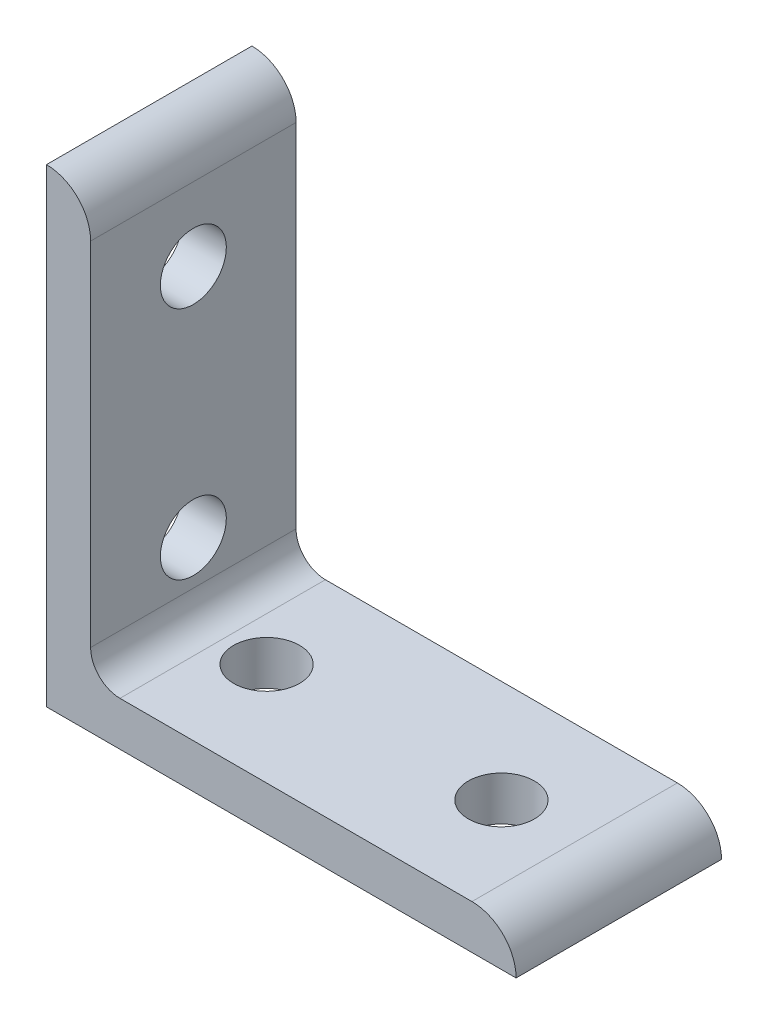
SolidWorks part; units mm, degrees
ref_plane "Front Plane" through (0, 0, 0) normal (0, 0, 1) x (1, 0, 0)
ref_plane "Top Plane" through (0, 0, 0) normal (0, 1, 0) x (1, 0, 0)
ref_plane "Right Plane" through (0, 0, 0) normal (1, 0, 0) x (0, 0, -1)
sketch "Sketch1" plane through (0, 0, 0) normal (0, 0, 1) x (1, 0, 0)
  line L0 (0, 0) -> (0, 50.8)
  line L1 (4.7752, 46.0248) -> (4.7752, 50.8) construction
  line L2 (4.7752, 46.0248) -> (4.7752, 7.9502)
  line L3 (7.9502, 4.7752) -> (46.0248, 4.7752)
  line L4 (4.7752, 50.8) -> (0, 50.8) construction
  line L5 (50.8, 0) -> (0, 0)
  line L6 (46.0248, 4.7752) -> (50.8, 4.7752) construction
  line L7 (50.8, 4.7752) -> (50.8, 0) construction
  arc A0 (4.7752, 46.0248) -> (0, 50.8) centre (0, 46.0248) ccw
  arc A1 (50.8, 0) -> (46.0248, 4.7752) centre (46.0248, 0) ccw
  arc A2 (4.7752, 7.9502) -> (7.9502, 4.7752) centre (7.9502, 7.9502) ccw
  point P10 (4.7752, 48.4124)
  dimension "E" = 3.175
  dimension "D" = 4.7752
  dimension "C" = 50.8
  dimension "B" = 50.8
extrude "Boss-Extrude1" add sketch "Sketch1" along normal mid plane 22.225
sketch "Sketch2" plane through (0, 0, 0) normal (0, 1, 0) x (1, 0, 0)
  line L0 (0, 0) -> (12.7, 0) construction
  line L1 (12.7, 0) -> (38.1, 0) construction
  circle A0 centre (12.7, 0) radius 3.5687
  circle A1 centre (38.1, 0) radius 3.5687
  dimension "D1" = 12.7
  dimension "E" = 7.1374
  dimension "D2" = 25.4
extrude "Cut-Extrude1" cut sketch "Sketch2" along normal through all
sketch "Sketch3" plane through (0, 0, 0) normal (1, 0, 0) x (0, 0, -1)
  line L0 (0, 0) -> (0, 12.7) construction
  line L1 (0, 12.7) -> (0, 38.1) construction
  circle A0 centre (0, 12.7) radius 3.5687
  circle A1 centre (0, 38.1) radius 3.5687
  dimension "D1" = 12.7
  dimension "D2" = 25.4
  dimension "E" = 7.1374
extrude "Cut-Extrude2" cut sketch "Sketch3" along normal through all
equation "\"E@Sketch3\" = \"E@Sketch2\""
equation "\"D1@Sketch3\" = \"D1@Sketch2\""
equation "\"D2@Sketch3\" = \"D2@Sketch2\""
